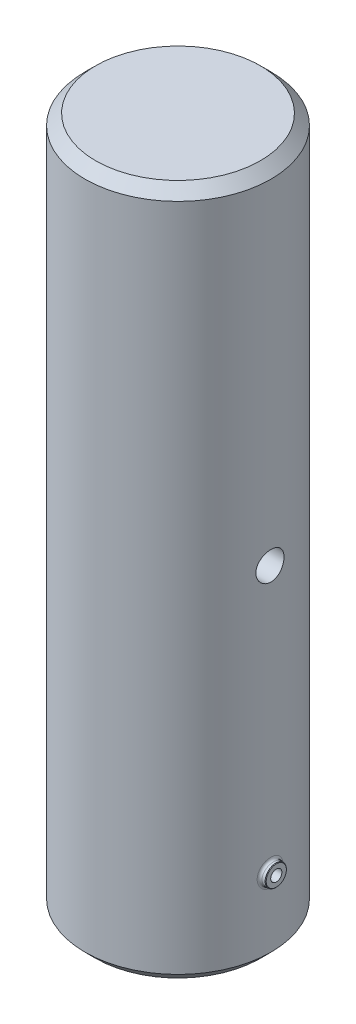
SolidWorks part; units mm, degrees
ref_plane "Plan de face" through (0, 0, 0) normal (0, 0, 1) x (1, 0, 0)
ref_plane "Plan de dessus" through (0, 0, 0) normal (0, 1, 0) x (1, 0, 0)
ref_plane "Plan de droite" through (0, 0, 0) normal (1, 0, 0) x (0, 0, -1)
sketch "Esquisse1" plane through (0, 0, 0) normal (0, 1, 0) x (1, 0, 0)
  circle A0 centre (0, 0) radius 17.5
  circle A1 centre (0, 0) radius 12.5
  dimension "D1" = 35
  dimension "D2" = 25
extrude "Boss.-Extru.1" add sketch "Esquisse1" along normal mid plane 130
ref_plane "Plan1" through (17.5, 0, 0) normal (1, 0, 0) x (0, 0, -1)
sketch "Esquisse3" plane through (17.5, 0, 0) normal (1, 0, 0) x (0, 0, -1)
  circle A0 centre (0, 0) radius 2.65
  dimension "D1" = 5.3
extrude "Enlèv. mat.-Extru.1" cut sketch "Esquisse3" against normal blind 4
mirror "Symétrie1" about plane through (0, 0, 0) normal (1, 0, 0) of "Enlèv. mat.-Extru.1"
sketch "Esquisse4" plane through (17.5, 0, 0) normal (1, 0, 0) x (0, 0, -1)
  circle A0 centre (0, -50) radius 2
  dimension "D1" = 4
  dimension "D2" = 50
extrude "Boss.-Extru.2" add sketch "Esquisse4" along normal blind 1 and the other way blind 2
sketch "Esquisse5" plane through (18.5, 0, 0) normal (1, 0, 0) x (0, 0, -1)
  circle A0 centre (0, -50) radius 1.05
  dimension "D1" = 2.1
extrude "Enlèv. mat.-Extru.2" cut sketch "Esquisse5" against normal up to next
sketch "Esquisse6" plane through (18.5, 0, 0) normal (1, 0, 0) x (0, 0, -1)
  circle A0 centre (0, -50) radius 2.5
  dimension "D1" = 5
extrude "Enlèv. mat.-Extru.3" cut sketch "Esquisse6" against normal blind 5 from offset 3.5 offset against normal yes
fillet "Congé1" radius 0.5 1 edges at (17.391, -49.5546, 1.9498)
chamfer "Chanfrein1" distance 0.1 angle 45 1 edges at (18.5, -50, -2)
sketch "Esquisse7" plane through (0, 65, 0) normal (0, 1, 0) x (1, 0, 0)
  circle A0 centre (0, 0) radius 17.5
  circle A1 centre (0, 0) radius 17.5 construction
extrude "Boss.-Extru.3" add sketch "Esquisse7" against normal blind 5
chamfer "Chanfrein2" distance 2 angle 45 2 edges at (0, 65, 17.5) (0, -65, 17.5)
chamfer "Chanfrein3" distance 1 angle 30 1 edges at (0, -65, 12.5)
